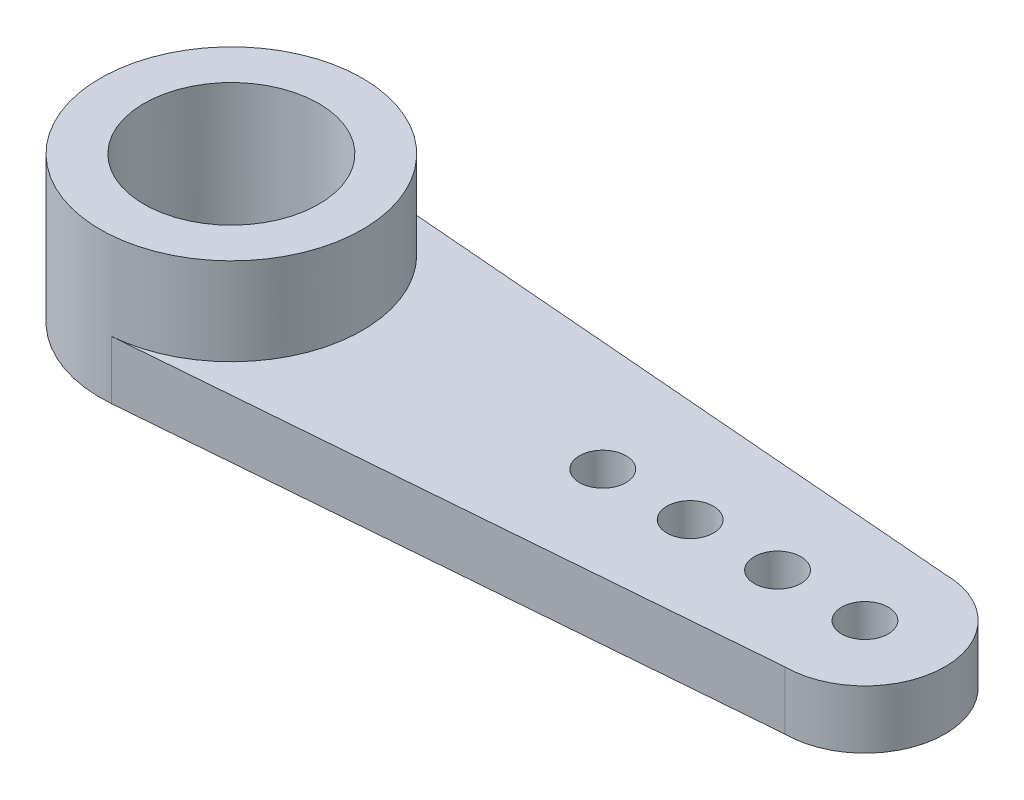
SolidWorks part; units mm, degrees
ref_plane "前基準面" through (0, 0, 0) normal (0, 0, 1) x (1, 0, 0)
ref_plane "上基準面" through (0, 0, 0) normal (0, 1, 0) x (1, 0, 0)
ref_plane "右基準面" through (0, 0, 0) normal (1, 0, 0) x (0, 0, -1)
sketch "草圖1" plane through (0, 0, 0) normal (0, 1, 0) x (1, 0, 0)
  line L0 (0.3639, 4.4853) -> (21.75, 2.75)
  line L1 (0, 0) -> (0, 21.3437) construction
  line L2 (0, 0) -> (21.75, 0) construction
  line L3 (0.3639, -4.4853) -> (21.75, -2.75)
  circle A0 centre (0, 0) radius 3
  arc A1 (0.3639, 4.4853) -> (0.3639, -4.4853) centre (0, 0) ccw
  circle A2 centre (12.75, 0) radius 0.8
  circle A3 centre (15.75, 0) radius 0.8
  circle A4 centre (18.75, 0) radius 0.8
  arc A5 (21.75, -2.75) -> (21.75, 2.75) centre (21.75, 0) ccw
  circle A6 centre (21.75, 0) radius 0.8
  point P3 (24.5, 0)
  dimension "D1" = 6
  dimension "D2" = 9
  dimension "D3" = 1.6
  dimension "D4" = 4
  dimension "D5" = 12.75
  dimension "D6" = 15.75
  dimension "D7" = 18.75
  dimension "D8" = 21.75
  dimension "D9" = 24.5
extrude "伸長1" add sketch "草圖1" along normal blind 2
sketch "草圖2" plane through (0, 2, 0) normal (0, -1, 0) x (1, 0, 0)
  circle A0 centre (0, 0) radius 4.5
  circle A1 centre (0, 0) radius 3
  arc A3 (0.3639, 4.4853) -> (0.3639, -4.4853) centre (0, 0) ccw construction
  circle A4 centre (0, 0) radius 3 construction
extrude "伸長2" add sketch "草圖2" against normal blind 3
